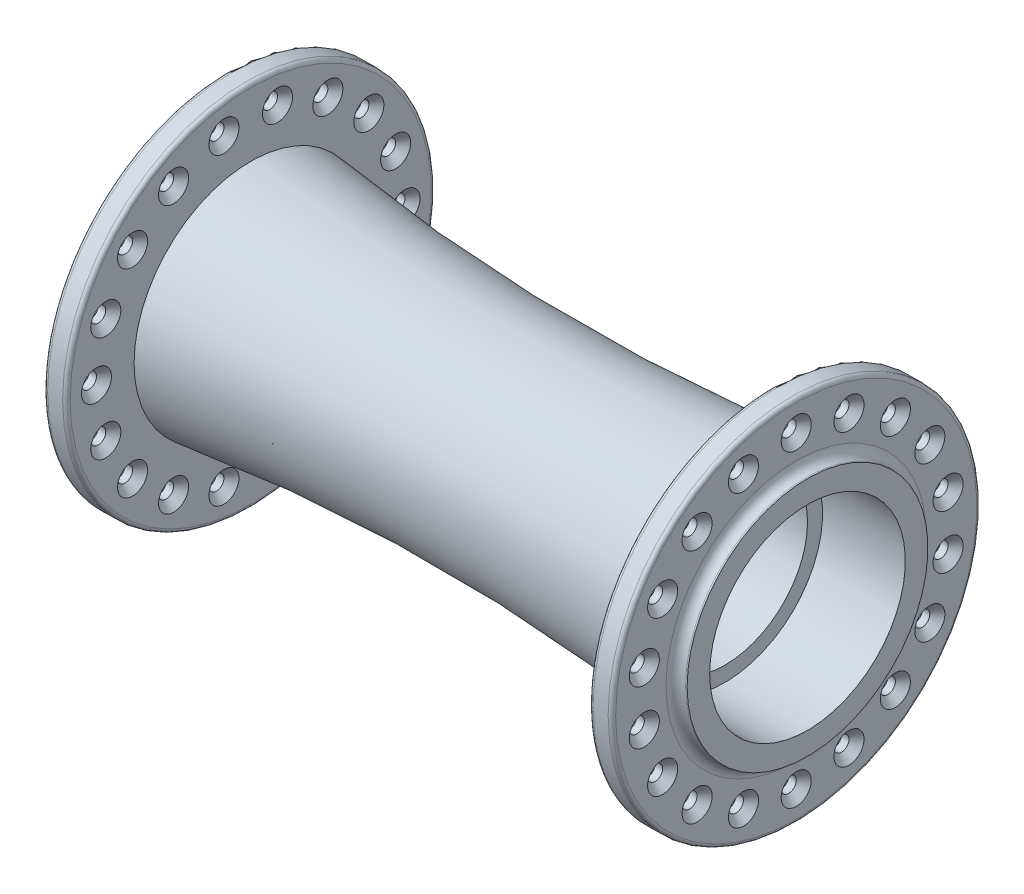
SolidWorks part; units mm, degrees
ref_plane "Plan de face" through (0, 0, 0) normal (0, 0, 1) x (1, 0, 0)
ref_plane "Plan de dessus" through (0, 0, 0) normal (0, 1, 0) x (1, 0, 0)
ref_plane "Plan de droite" through (0, 0, 0) normal (1, 0, 0) x (0, 0, -1)
sketch "Esquisse1" plane through (0, 0, 0) normal (0, 0, 1) x (1, 0, 0)
  line L0 (-56.1645, 0) -> (40.9334, 0) construction
  line L1 (0, 0) -> (0, 34.841) construction
  line L2 (-39.25, 11) -> (39.25, 11)
  line L3 (-39.25, 11) -> (-39.25, 16)
  line L4 (-39.25, 16) -> (-39.05, 16)
  line L5 (-37.75, 17.3) -> (-37.75, 24.5)
  line L6 (-37.75, 24.5) -> (-34.75, 24.5)
  line L7 (-34.75, 24.5) -> (-34.75, 15.5)
  line L8 (39.25, 11) -> (39.25, 16)
  line L9 (39.25, 16) -> (39.05, 16)
  line L10 (37.75, 17.3) -> (37.75, 24.5)
  line L11 (37.75, 24.5) -> (34.75, 24.5)
  line L12 (34.75, 24.5) -> (34.75, 15.5)
  arc A0 (-34.75, 15.5) -> (34.75, 15.5) centre (0, 283.2544) ccw
  arc A2 (-39.05, 16) -> (-37.75, 17.3) centre (-39.05, 17.3) ccw
  arc A3 (37.75, 17.3) -> (39.05, 16) centre (39.05, 17.3) ccw
  point P19 (-37.75, 16)
  point P23 (37.75, 16)
  dimension "D6" = 1.3
  dimension "D9" = 270
  dimension "D1" = 3
  dimension "D3" = 32
  dimension "D4" = 49
  dimension "D5" = 31
  dimension "D7" = 78.5
  dimension "D8" = 75.5
  dimension "D10" = 22
revolve "Révolution1" add sketch "Esquisse1" angle 360 about L0
fillet "Congé1" radius 0.5 4 edges at (34.75, 0, 24.5) (37.75, 0, 24.5) (-37.75, 0, 24.5) (-34.75, 0, 24.5)
sketch "Esquisse2" plane through (37.75, 0, 0) normal (1, 0, 0) x (0, 0, -1)
  circle A0 centre (0, 20.5) radius 1
  circle A1 centre (0, 0) radius 20.5 construction
  dimension "D1" = 2
  dimension "D2" = 41
extrude "Enlèv. mat.-Extru.1" cut sketch "Esquisse2" against normal up to next (3 mm away)
sketch "Esquisse3" plane through (-37.75, 0, 0) normal (-1, 0, 0) x (0, 0, 1)
  line L0 (0, 0) -> (-3.5598, 20.1886) construction
  line L1 (0, -26.95) -> (0, 26.95) construction
  circle A0 centre (-3.5598, 20.1886) radius 1
  circle A1 centre (0, 20.5) radius 1 construction
  circle A2 centre (0, 0) radius 20.5 construction
  dimension "D1" = 10
extrude "Enlèv. mat.-Extru.2" cut sketch "Esquisse3" against normal up to next (3 mm away)
chamfer "Chanfrein1" distance 1 angle 45 4 edges at (37.75, 20.5, -1) (34.75, 20.5, -1) (-34.75, 20.1886, -2.5598) (-37.75, 20.1886, -2.5598)
pattern_circular "Répétition circulaire1" count 18 every 20 about axis through (0, 0, 0) along (1, 0, 0) of "Enlèv. mat.-Extru.1", "Chanfrein1", "Enlèv. mat.-Extru.2"
sketch "Esquisse4" plane through (0, 0, 0) normal (0, 0, 1) x (1, 0, 0)
  line L0 (-42.4958, 0) -> (43.9223, 0) construction
  line L2 (-39.25, 13) -> (-28.25, 13)
  line L3 (-39.25, 13) -> (-39.25, 0)
  line L4 (-39.25, 0) -> (-28.25, 0)
  line L5 (-28.25, 13) -> (-28.25, 0)
  line L6 (0, -17.2955) -> (0, 22.288) construction
  line L7 (28.25, 13) -> (28.25, 0)
  line L8 (39.25, 0) -> (28.25, 0)
  line L9 (39.25, 13) -> (39.25, 0)
  line L10 (39.25, 13) -> (28.25, 13)
  line L12 (-39.25, 11) -> (-39.25, -11) construction
  dimension "D1" = 26
  dimension "D2" = 11
revolve "Enlèvement de matière-Révolution3" cut sketch "Esquisse4" angle 360 about L0
